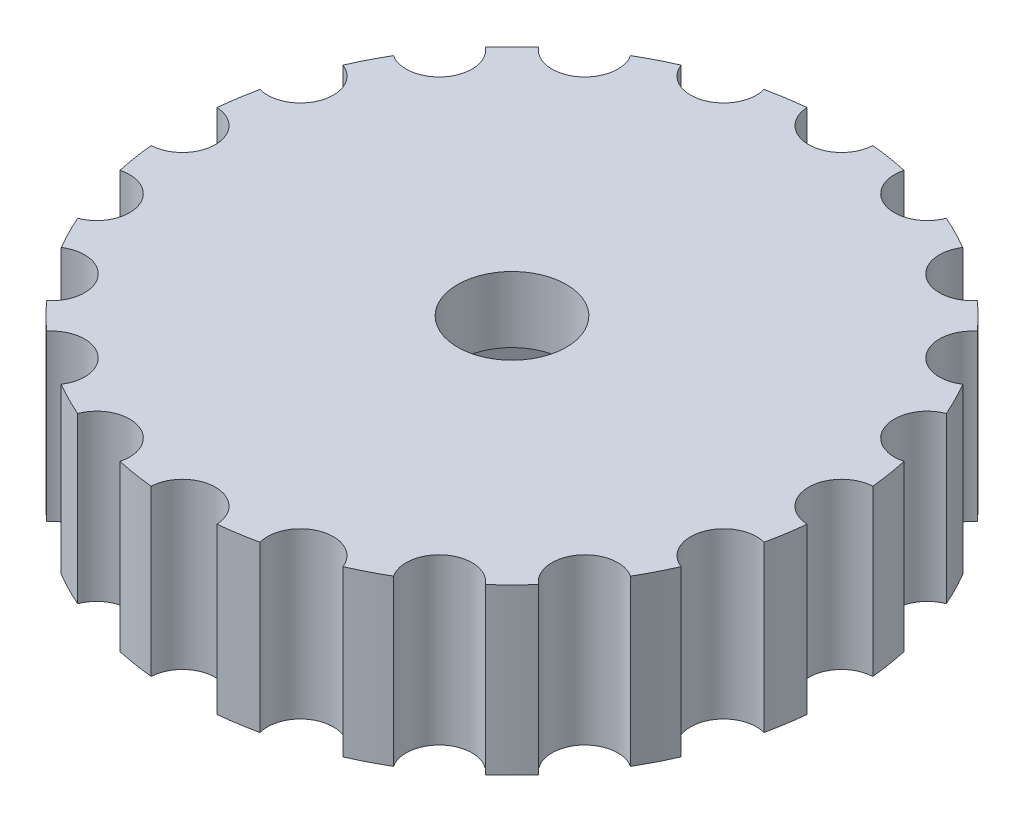
SolidWorks part; units mm, degrees
ref_plane "Plano frontal" through (0, 0, 0) normal (0, 0, 1) x (1, 0, 0)
ref_plane "Plano superior" through (0, 0, 0) normal (0, 1, 0) x (1, 0, 0)
ref_plane "Plano direito" through (0, 0, 0) normal (1, 0, 0) x (0, 0, -1)
sketch "Esboço1" plane through (0, 0, 0) normal (0, 0, 1) x (1, 0, 0)
  line L0 (-1.65, 5) -> (-10, 5)
  line L1 (-10, 5) -> (-10, 0)
  line L3 (-10, 0) -> (-1.65, 0)
  line L6 (-1.65, 0) -> (-1.65, 5)
  line L7 (0, 0) -> (0, 13.2193) construction
  dimension "D1" = 3.3
  dimension "D2" = 20
  dimension "D3" = 5
revolve "Revolução1" add sketch "Esboço1" angle 360 about L7
sketch "Esboço3" plane through (0, 0, 0) normal (0, -1, 0) x (1, 0, 0)
  line L1 (3.1754, 0) -> (1.5877, 2.75)
  line L2 (1.5877, 2.75) -> (-1.5877, 2.75)
  line L3 (-1.5877, 2.75) -> (-3.1754, 0)
  line L4 (-3.1754, 0) -> (-1.5877, -2.75)
  line L5 (-1.5877, -2.75) -> (1.5877, -2.75)
  line L6 (1.5877, -2.75) -> (3.1754, 0)
  circle A0 centre (0, 0) radius 2.75 construction
  dimension "D1" = 5.5
extrude "Corte-extrusão1" cut sketch "Esboço3" against normal blind 3
sketch "Esboço4" plane through (0, 5, 0) normal (0, 1, 0) x (1, 0, 0)
  circle A0 centre (0, 10) radius 1
  circle A1 centre (0, 0) radius 10 construction
  circle A2 centre (3.0902, 9.5106) radius 1
  circle A3 centre (5.8779, 8.0902) radius 1
  circle A4 centre (8.0902, 5.8779) radius 1
  circle A5 centre (9.5106, 3.0902) radius 1
  circle A6 centre (10, 0) radius 1
  circle A7 centre (9.5106, -3.0902) radius 1
  circle A8 centre (8.0902, -5.8779) radius 1
  circle A9 centre (5.8779, -8.0902) radius 1
  circle A10 centre (3.0902, -9.5106) radius 1
  circle A11 centre (0, -10) radius 1
  circle A12 centre (-3.0902, -9.5106) radius 1
  circle A13 centre (-5.8779, -8.0902) radius 1
  circle A14 centre (-8.0902, -5.8779) radius 1
  circle A15 centre (-9.5106, -3.0902) radius 1
  circle A16 centre (-10, 0) radius 1
  circle A17 centre (-9.5106, 3.0902) radius 1
  circle A18 centre (-8.0902, 5.8779) radius 1
  circle A19 centre (-5.8779, 8.0902) radius 1
  circle A20 centre (-3.0902, 9.5106) radius 1
  point P36 (0, 0)
  dimension "D1" = 2
  dimension "D2" = 20
extrude "Corte-extrusão2" cut sketch "Esboço4" against normal blind 10
